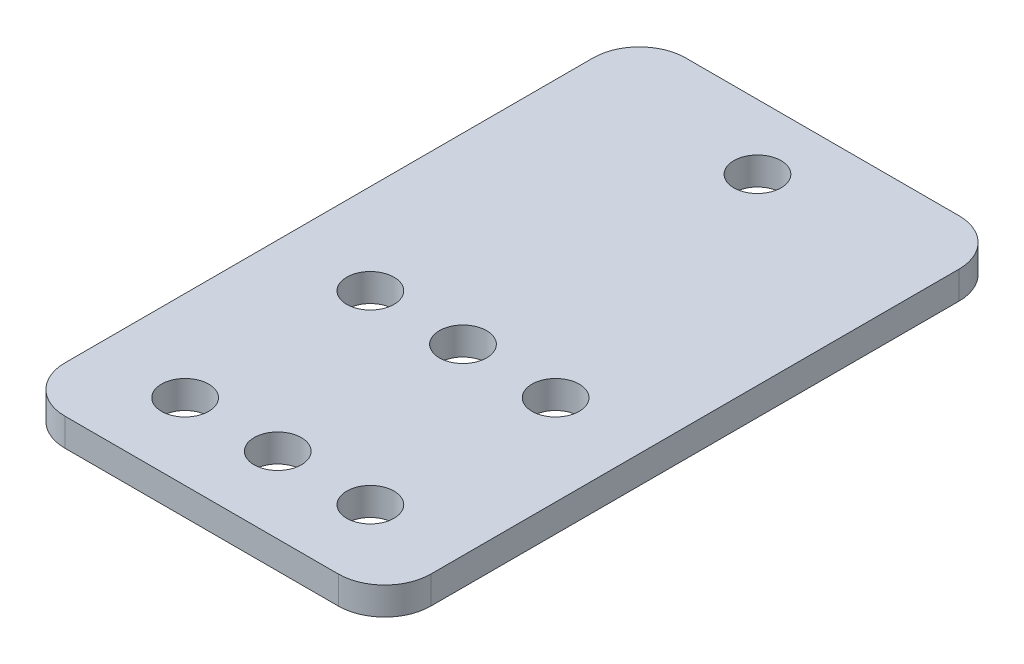
SolidWorks part; units mm, degrees
material "6061-T6 (SS)"
ref_plane "Front Plane" through (0, 0, 0) normal (0, 0, 1) x (1, 0, 0)
ref_plane "Top Plane" through (0, 0, 0) normal (0, 1, 0) x (1, 0, 0)
ref_plane "Right Plane" through (0, 0, 0) normal (1, 0, 0) x (0, 0, -1)
sketch "Sketch1" plane through (0, 0, 0) normal (0, 1, 0) x (1, 0, 0)
  line L0 (-19.75, 0) -> (0, 0) construction
  line L1 (14.75, -33.5) -> (-14.75, -33.5)
  line L2 (19.75, -28.5) -> (19.75, 28.5)
  line L3 (14.75, 33.5) -> (-14.75, 33.5)
  line L4 (-19.75, -28.5) -> (-19.75, 28.5)
  line L5 (0, 33.5) -> (0, 0) construction
  line L9 (10, -25.29) -> (0, -25.29) construction
  arc A0 (-14.75, -33.5) -> (-19.75, -28.5) centre (-14.75, -28.5) cw
  arc A1 (14.75, -33.5) -> (19.75, -28.5) centre (14.75, -28.5) ccw
  arc A2 (19.75, 28.5) -> (14.75, 33.5) centre (14.75, 28.5) ccw
  arc A3 (-14.75, 33.5) -> (-19.75, 28.5) centre (-14.75, 28.5) ccw
  circle A4 centre (0, 26.5) radius 2.55
  circle A7 centre (10, -25.29) radius 2.55
  circle A8 centre (10, -5.29) radius 2.55
  circle A9 centre (0, -25.29) radius 2.55
  circle A10 centre (0, -5.29) radius 2.55
  circle A11 centre (-10, -25.29) radius 2.55
  circle A12 centre (-10, -5.29) radius 2.55
  dimension "D2" = 5
  dimension "D3" = 7
  dimension "D7" = 20
  dimension "D10" = 3
  dimension "D8" = 9.75
  dimension "D6" = 5.1
  dimension "D1" = 67
  dimension "D9" = 39.5
  dimension "D11" = 10
  dimension "D12" = 8.21
extrude "Boss-Extrude1" add sketch "Sketch1" along normal blind 3
